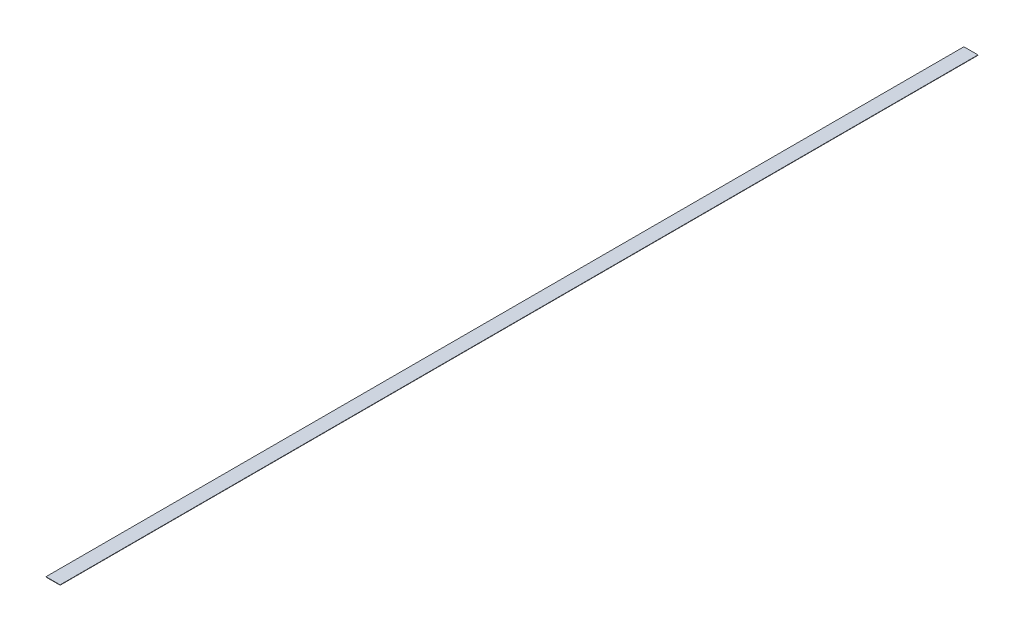
SolidWorks part; units mm, degrees
ref_plane "Front Plane" through (0, 0, 0) normal (0, 0, 1) x (1, 0, 0)
ref_plane "Top Plane" through (0, 0, 0) normal (0, 1, 0) x (1, 0, 0)
ref_plane "Right Plane" through (0, 0, 0) normal (1, 0, 0) x (0, 0, -1)
sketch "Sketch1" plane through (0, 0, 0) normal (0, 1, 0) x (1, 0, 0)
  line L1 (-25.4, -1651) -> (25.4, -1651)
  line L2 (-25.4, -1651) -> (-25.4, 1651)
  line L3 (-25.4, 1651) -> (25.4, 1651)
  line L4 (25.4, -1651) -> (25.4, 1651)
  line L5 (-25.4, -1651) -> (25.4, 1651) construction
  line L6 (-25.4, 1651) -> (25.4, -1651) construction
  point P1 (0, 0)
  dimension "D1" = 3302
  dimension "D2" = 50.8
extrude "Boss-Extrude1" add sketch "Sketch1" along normal blind 1.27
